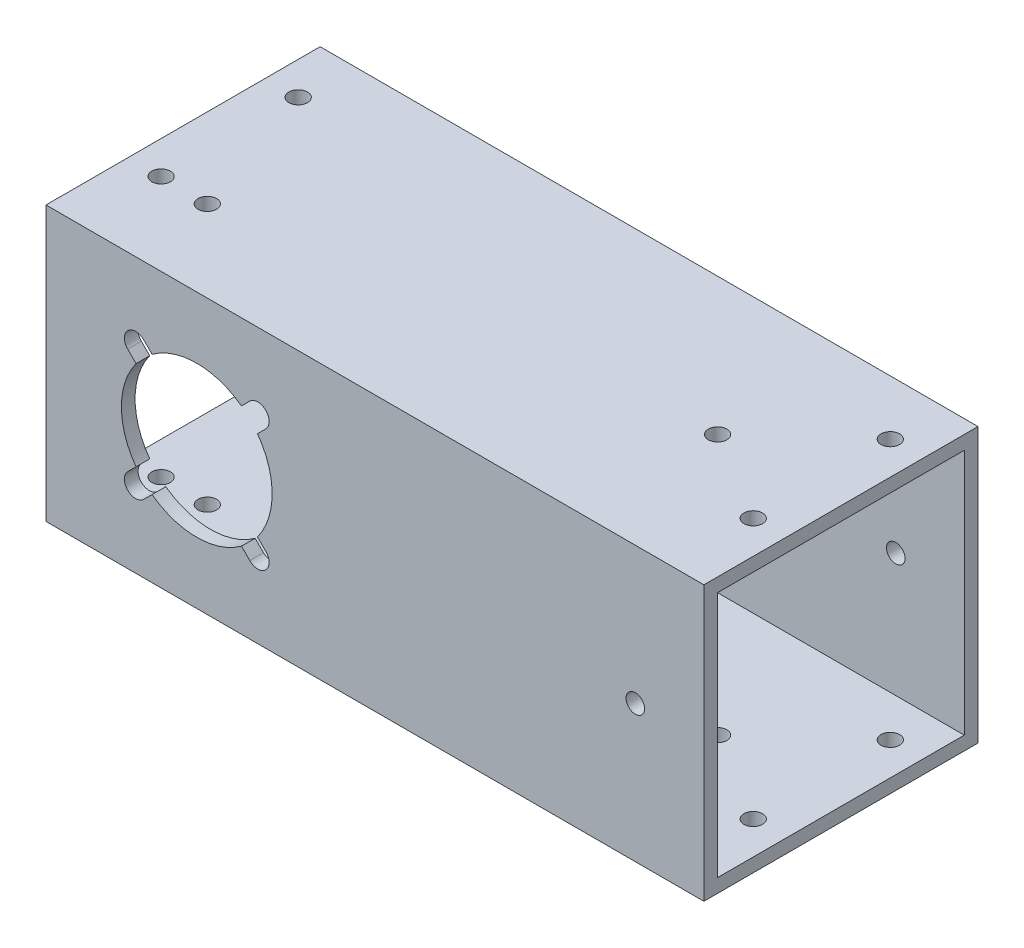
SolidWorks part; units mm, degrees
material "6061-T6 (SS)"
ref_plane "Front Plane" through (0, 0, 0) normal (0, 0, 1) x (1, 0, 0)
ref_plane "Top Plane" through (0, 0, 0) normal (0, 1, 0) x (1, 0, 0)
ref_plane "Right Plane" through (0, 0, 0) normal (1, 0, 0) x (0, 0, -1)
sketch "Sketch1" plane through (0, 0, 0) normal (1, 0, 0) x (0, 0, -1)
  line L1 (-31.75, -31.75) -> (31.75, -31.75)
  line L2 (-31.75, -31.75) -> (-31.75, 31.75)
  line L3 (-31.75, 31.75) -> (31.75, 31.75)
  line L4 (31.75, -31.75) -> (31.75, 31.75)
  point P0 (0, 0)
  dimension "D1" = 63.5
extrude "Boss-Extrude1" add sketch "Sketch1" along normal blind 704.85
sketch "Sketch2" plane through (704.85, 0, 0) normal (1, 0, 0) x (0, 0, -1)
  line L0 (31.75, 31.75) -> (-31.75, 31.75) construction
  line L1 (-28.575, -28.575) -> (28.575, -28.575)
  line L2 (-28.575, -28.575) -> (-28.575, 28.575)
  line L3 (-28.575, 28.575) -> (28.575, 28.575)
  line L4 (28.575, -28.575) -> (28.575, 28.575)
  line L5 (-28.575, -28.575) -> (28.575, 28.575) construction
  line L6 (-28.575, 28.575) -> (28.575, -28.575) construction
  point P0 (0, 0)
  dimension "D1" = 3.175
extrude "Cut-Extrude1" cut sketch "Sketch2" against normal through all
sketch "Sketch3" plane through (0, 0, 31.75) normal (0, 0, 1) x (1, 0, 0)
  line L0 (0, 0) -> (704.85, 0) construction
  line L1 (704.85, 31.75) -> (704.85, -31.75) construction
  line L2 (352.425, -31.75) -> (352.425, 31.75) construction
  line L3 (704.85, -31.75) -> (0, -31.75) construction
  line L4 (704.85, 31.75) -> (0, 31.75) construction
  circle A0 centre (352.425, 0) radius 17.4625
  circle A1 centre (34.925, 0) radius 17.4625
  circle A2 centre (669.925, 0) radius 17.4625
  dimension "D1" = 34.925
  dimension "D2" = 317.5
  dimension "D3" = 317.5
extrude "Cut-Extrude2" cut sketch "Sketch3" against normal up to next
sketch "Sketch8" plane through (0, 31.75, 0) normal (0, 1, 0) x (1, 0, 0)
  line L0 (0, 0) -> (704.85, 0) construction
  line L1 (704.85, 31.75) -> (704.85, -31.75) construction
  line L2 (352.425, 0) -> (352.425, 31.75) construction
  line L3 (704.85, 31.75) -> (0, 31.75) construction
  circle A0 centre (466.725, 0) radius 2.1526
  circle A1 centre (123.825, 0) radius 2.1526
  circle A2 centre (581.025, 0) radius 2.1526
  circle A3 centre (238.125, 0) radius 2.1526
  dimension "D1" = 4.3053
  dimension "D2" = 114.3
  dimension "D3" = 228.6
extrude "Cut-Extrude6" cut sketch "Sketch8" against normal through all
sketch "Sketch10" plane through (0, 0, 31.75) normal (0, 0, 1) x (1, 0, 0)
  line L0 (0, 0) -> (704.85, 0) construction
  line L1 (704.85, 31.75) -> (704.85, -31.75) construction
  line L2 (352.425, 0) -> (352.425, 31.75) construction
  line L3 (704.85, 31.75) -> (0, 31.75) construction
  circle A0 centre (225.425, 0) radius 2.1527
  circle A1 centre (568.325, 0) radius 2.1526
  circle A2 centre (136.525, 0) radius 2.1527
  circle A3 centre (479.425, 0) radius 2.1526
  dimension "D1" = 4.3053
  dimension "D2" = 127
  dimension "D3" = 215.9
extrude "Cut-Extrude7" cut sketch "Sketch10" against normal through all
sketch "Sketch13" plane through (0, 0, -31.75) normal (0, 0, -1) x (-1, 0, 0)
  line L0 (0, 0) -> (-704.85, 0) construction
  line L1 (-704.85, -31.75) -> (-704.85, 31.75) construction
  line L2 (-352.425, 0) -> (-34.925, 0) construction
  line L3 (-352.425, 0) -> (-669.925, 0) construction
  circle A0 centre (-352.425, 0) radius 16
  circle A1 centre (-34.925, 0) radius 16
  circle A2 centre (-669.925, 0) radius 16
  dimension "D3" = 32
  dimension "D1" = 317.5
  dimension "D2" = 317.5
extrude "Cut-Extrude9" cut sketch "Sketch13" against normal up to next
sketch "Sketch14" plane through (0, 0, -31.75) normal (0, 0, -1) x (-1, 0, 0)
  line L0 (0, 0) -> (-704.85, 0) construction
  line L1 (-704.85, -31.75) -> (-704.85, 31.75) construction
  line L2 (-352.425, 0) -> (-34.925, 0) construction
  line L3 (-669.925, 0) -> (-352.425, 0) construction
  line L4 (-352.425, 0) -> (-338.2829, 14.1421) construction
  line L5 (-669.925, 0) -> (-655.7829, 14.1421) construction
  line L6 (-34.925, 0) -> (-20.7829, 14.1421) construction
  line L7 (-352.425, 0) -> (-338.2829, -14.1421) construction
  line L8 (-352.425, 0) -> (-366.5671, -14.1421) construction
  line L9 (-352.425, 0) -> (-366.5671, 14.1421) construction
  line L10 (-34.925, 0) -> (-20.7829, -14.1421) construction
  line L11 (-34.925, 0) -> (-49.0671, -14.1421) construction
  line L12 (-34.925, 0) -> (-49.0671, 14.1421) construction
  line L13 (-669.925, 0) -> (-655.7829, -14.1421) construction
  line L14 (-669.925, 0) -> (-684.0671, -14.1421) construction
  line L15 (-669.925, 0) -> (-684.0671, 14.1421) construction
  circle A0 centre (-655.7829, 14.1421) radius 2.625
  circle A1 centre (-338.2829, 14.1421) radius 2.625
  circle A2 centre (-20.7829, 14.1421) radius 2.625
  circle A3 centre (-352.425, 0) radius 16
  circle A4 centre (-34.925, 0) radius 16
  circle A5 centre (-669.925, 0) radius 16
  circle A6 centre (-338.2829, -14.1421) radius 2.625
  circle A7 centre (-366.5671, -14.1421) radius 2.625
  circle A8 centre (-366.5671, 14.1421) radius 2.625
  circle A9 centre (-20.7829, -14.1421) radius 2.625
  circle A10 centre (-49.0671, -14.1421) radius 2.625
  circle A11 centre (-49.0671, 14.1421) radius 2.625
  circle A12 centre (-655.7829, -14.1421) radius 2.625
  circle A13 centre (-684.0671, -14.1421) radius 2.625
  circle A14 centre (-684.0671, 14.1421) radius 2.625
  point P28 (-352.425, 0)
  point P35 (-34.925, 0)
  point P42 (-669.925, 0)
  dimension "D4" = 5.25
  dimension "D1" = 45
  dimension "D2" = 45
  dimension "D3" = 45
  dimension "D5" = 20
  dimension "D6" = 4
  dimension "D7" = 4
  dimension "D8" = 4
extrude "Cut-Extrude10" cut sketch "Sketch14" against normal up to next (3.175 mm away)
sketch "Sketch15" plane through (0, 0, 31.75) normal (0, 0, 1) x (1, 0, 0)
  line L0 (0, 0) -> (704.85, 0) construction
  line L1 (50.9233, 12.286) -> (47.211, 15.9983) construction
  line L2 (0, 31.75) -> (0, -31.75) construction
  line L3 (704.85, 31.75) -> (704.85, -31.75) construction
  line L4 (352.425, 0) -> (352.425, 31.75) construction
  line L5 (704.85, 31.75) -> (0, 31.75) construction
  line L6 (34.925, 0) -> (352.425, 0) construction
  line L7 (193.675, 0) -> (193.675, 31.75) construction
  line L8 (669.925, 0) -> (352.425, 0) construction
  line L9 (511.175, 0) -> (511.175, 31.75) construction
  line L10 (352.425, 0) -> (366.5671, 14.1421) construction
  line L11 (364.711, -15.9983) -> (362.7764, -14.0637)
  line L12 (49.0671, 14.1421) -> (50.9233, 12.286) construction
  line L13 (366.5671, 14.1421) -> (364.711, 15.9983) construction
  line L14 (364.711, 15.9983) -> (368.4233, 12.286) construction
  line L15 (368.4233, 12.286) -> (366.4887, 10.3514)
  line L16 (364.711, 15.9983) -> (362.7764, 14.0637)
  line L17 (368.4233, -12.286) -> (366.4887, -10.3514)
  line L18 (352.425, 0) -> (366.5671, -14.1421) construction
  line L19 (366.5671, -14.1421) -> (368.4233, -12.286) construction
  line L20 (368.4233, -12.286) -> (364.711, -15.9983) construction
  line L21 (336.4267, -12.286) -> (338.3613, -10.3514)
  line L22 (340.139, -15.9983) -> (342.0736, -14.0637)
  line L23 (352.425, 0) -> (338.2829, -14.1421) construction
  line L24 (338.2829, -14.1421) -> (340.139, -15.9983) construction
  line L25 (340.139, -15.9983) -> (336.4267, -12.286) construction
  line L26 (340.139, 15.9983) -> (342.0736, 14.0637)
  line L27 (336.4267, 12.286) -> (338.3613, 10.3514)
  line L28 (352.425, 0) -> (338.2829, 14.1421) construction
  line L29 (338.2829, 14.1421) -> (336.4267, 12.286) construction
  line L30 (336.4267, 12.286) -> (340.139, 15.9983) construction
  line L31 (34.925, 0) -> (49.0671, 14.1421) construction
  line L32 (47.211, -15.9983) -> (50.9233, -12.286) construction
  line L33 (49.0671, -14.1421) -> (47.211, -15.9983) construction
  line L34 (34.925, 0) -> (49.0671, -14.1421) construction
  line L35 (18.9267, -12.286) -> (22.639, -15.9983) construction
  line L36 (20.7829, -14.1421) -> (18.9267, -12.286) construction
  line L37 (34.925, 0) -> (20.7829, -14.1421) construction
  line L38 (22.639, 15.9983) -> (18.9267, 12.286) construction
  line L39 (20.7829, 14.1421) -> (22.639, 15.9983) construction
  line L40 (34.925, 0) -> (20.7829, 14.1421) construction
  line L41 (34.925, 0) -> (34.925, 31.75) construction
  line L42 (50.9233, 12.286) -> (48.9887, 10.3514)
  line L43 (47.211, 15.9983) -> (45.2764, 14.0637)
  line L44 (47.211, -15.9983) -> (45.2764, -14.0637)
  line L45 (50.9233, -12.286) -> (48.9887, -10.3514)
  line L46 (18.9267, -12.286) -> (20.8613, -10.3514)
  line L47 (22.639, 15.9983) -> (24.5736, 14.0637)
  line L48 (18.9267, 12.286) -> (20.8613, 10.3514)
  line L49 (22.639, -15.9983) -> (24.5736, -14.0637)
  line L50 (685.9233, 12.286) -> (682.211, 15.9983) construction
  line L51 (684.0671, 14.1421) -> (685.9233, 12.286) construction
  line L52 (669.925, 0) -> (684.0671, 14.1421) construction
  line L53 (682.211, -15.9983) -> (685.9233, -12.286) construction
  line L54 (684.0671, -14.1421) -> (682.211, -15.9983) construction
  line L55 (669.925, 0) -> (684.0671, -14.1421) construction
  line L56 (653.9267, -12.286) -> (657.639, -15.9983) construction
  line L57 (655.7829, -14.1421) -> (653.9267, -12.286) construction
  line L58 (669.925, 0) -> (655.7829, -14.1421) construction
  line L59 (657.639, 15.9983) -> (653.9267, 12.286) construction
  line L60 (655.7829, 14.1421) -> (657.639, 15.9983) construction
  line L61 (669.925, 0) -> (655.7829, 14.1421) construction
  line L62 (669.925, 0) -> (669.925, 31.75) construction
  line L63 (685.9233, 12.286) -> (683.9887, 10.3514)
  line L64 (682.211, 15.9983) -> (680.2764, 14.0637)
  line L65 (682.211, -15.9983) -> (680.2764, -14.0637)
  line L66 (685.9233, -12.286) -> (683.9887, -10.3514)
  line L67 (653.9267, -12.286) -> (655.8613, -10.3514)
  line L68 (657.639, 15.9983) -> (659.5736, 14.0637)
  line L69 (653.9267, 12.286) -> (655.8613, 10.3514)
  line L70 (657.639, -15.9983) -> (659.5736, -14.0637)
  arc A0 (362.7764, 14.0637) -> (342.0736, 14.0637) centre (352.425, 0) ccw
  arc A1 (368.4233, 12.286) -> (364.711, 15.9983) centre (366.5671, 14.1421) ccw
  arc A2 (364.711, -15.9983) -> (368.4233, -12.286) centre (366.5671, -14.1421) ccw
  arc A3 (336.4267, -12.286) -> (340.139, -15.9983) centre (338.2829, -14.1421) ccw
  arc A4 (340.139, 15.9983) -> (336.4267, 12.286) centre (338.2829, 14.1421) ccw
  arc A5 (338.3613, 10.3514) -> (338.3613, -10.3514) centre (352.425, 0) ccw
  arc A6 (342.0736, -14.0637) -> (362.7764, -14.0637) centre (352.425, 0) ccw
  arc A7 (366.4887, -10.3514) -> (366.4887, 10.3514) centre (352.425, 0) ccw
  arc A8 (20.8613, -10.3514) -> (20.8613, 10.3514) centre (34.925, 0) cw
  arc A9 (45.2764, -14.0637) -> (24.5736, -14.0637) centre (34.925, 0) cw
  arc A10 (48.9887, 10.3514) -> (48.9887, -10.3514) centre (34.925, 0) cw
  arc A11 (47.211, 15.9983) -> (50.9233, 12.286) centre (49.0671, 14.1421) cw
  arc A13 (50.9233, -12.286) -> (47.211, -15.9983) centre (49.0671, -14.1421) cw
  arc A14 (22.639, -15.9983) -> (18.9267, -12.286) centre (20.7829, -14.1421) cw
  arc A15 (18.9267, 12.286) -> (22.639, 15.9983) centre (20.7829, 14.1421) cw
  arc A16 (24.5736, 14.0637) -> (45.2764, 14.0637) centre (34.925, 0) cw
  arc A17 (655.8613, -10.3514) -> (655.8613, 10.3514) centre (669.925, 0) cw
  arc A18 (680.2764, -14.0637) -> (659.5736, -14.0637) centre (669.925, 0) cw
  arc A19 (683.9887, 10.3514) -> (683.9887, -10.3514) centre (669.925, 0) cw
  arc A20 (682.211, 15.9983) -> (685.9233, 12.286) centre (684.0671, 14.1421) cw
  arc A21 (685.9233, -12.286) -> (682.211, -15.9983) centre (684.0671, -14.1421) cw
  arc A22 (657.639, -15.9983) -> (653.9267, -12.286) centre (655.7829, -14.1421) cw
  arc A23 (653.9267, 12.286) -> (657.639, 15.9983) centre (655.7829, 14.1421) cw
  arc A24 (659.5736, 14.0637) -> (680.2764, 14.0637) centre (669.925, 0) cw
  point P43 (352.425, 0)
  dimension "D2" = 45
  dimension "D3" = 5.25
  dimension "D7" = 17.4625
  dimension "D1" = 20
  dimension "D4" = 90
  dimension "D5" = 5.25
  dimension "D8" = 2.7359
  dimension "D6" = 4
extrude "Cut-Extrude11" cut sketch "Sketch15" against normal up to next
sketch "Sketch17" plane through (0, -31.75, 0) normal (0, -1, 0) x (1, 0, 0)
  line L0 (0, 0) -> (704.85, 0) construction
  line L1 (704.85, 31.75) -> (704.85, -31.75) construction
  line L2 (342.9, 0) -> (361.95, 0)
  line L3 (342.9, -25.4) -> (361.95, -25.4)
  line L4 (342.9, -25.4) -> (342.9, 0)
  line L6 (361.95, -25.4) -> (361.95, 0)
  line L7 (342.9, -25.4) -> (352.425, 0) construction
  line L8 (352.425, 0) -> (361.95, -25.4) construction
  point P5 (352.425, 0)
extrude "Cut-Extrude13" cut sketch "Sketch17" against normal up to next
sketch "Sketch18" plane through (704.85, 0, 0) normal (1, 0, 0) x (0, 0, -1)
  line L1 (-31.75, 31.75) -> (31.75, 31.75)
  line L2 (-31.75, 31.75) -> (-31.75, -31.75)
  line L3 (-31.75, -31.75) -> (31.75, -31.75)
  line L4 (31.75, 31.75) -> (31.75, -31.75)
extrude "Cut-Extrude14" cut sketch "Sketch18" against normal blind 552.45
hole_wizard "#8 Clearance Hole1" positions "Sketch20" profile "Sketch19" hole size "#8" standard "ANSI Inch" end condition through all
sketch "Sketch20" plane through (0, 31.75, 0) normal (0, 1, 0) x (1, 0, 0)
  line L0 (152.4, 31.75) -> (0, 31.75) construction
  line L1 (0, 31.75) -> (0, -31.75) construction
  line L2 (152.4, -31.75) -> (0, -31.75) construction
  line L3 (152.4, 31.75) -> (152.4, -31.75) construction
  point P0 (7.62, 19.05)
  point P2 (7.62, -12.7)
  point P4 (144.78, -12.7)
  point P6 (144.78, 19.05)
  dimension "D1" = 12.7
  dimension "D2" = 7.62
  dimension "D3" = 7.62
  dimension "D4" = 19.05
  dimension "D5" = 7.62
  dimension "D6" = 7.62
  dimension "D7" = 12.7
  dimension "D8" = 19.05
sketch "Sketch19" plane through (7.62, 31.75, -19.05) normal (1, 0, 0) x (0, 0, 1)
  line L0 (0, 0) -> (0, 63.5)
  line L1 (0, 63.5) -> (2.1526, 63.5)
  line L2 (2.1526, 63.5) -> (2.1526, 0)
  line L5 (2.1526, 0) -> (0, 0)
  line L11 (0, -6.35) -> (0, 107.95) construction
  dimension "Thru Hole Dia." = 4.3053
  dimension "Thru Hole Depth" = 63.5
sketch "Sketch21" plane through (0, 31.75, 0) normal (0, 1, 0) x (1, 0, 0)
  circle A0 centre (18.4785, -12.8587) radius 2.1526
extrude "Cut-Extrude15" cut sketch "Sketch21" against normal blind 6.35
sketch "Sketch22" plane through (0, -28.575, 0) normal (0, 1, 0) x (1, 0, 0)
  circle A0 centre (18.4785, -12.8587) radius 2.1526
extrude "Cut-Extrude16" cut sketch "Sketch22" against normal blind 6.35
